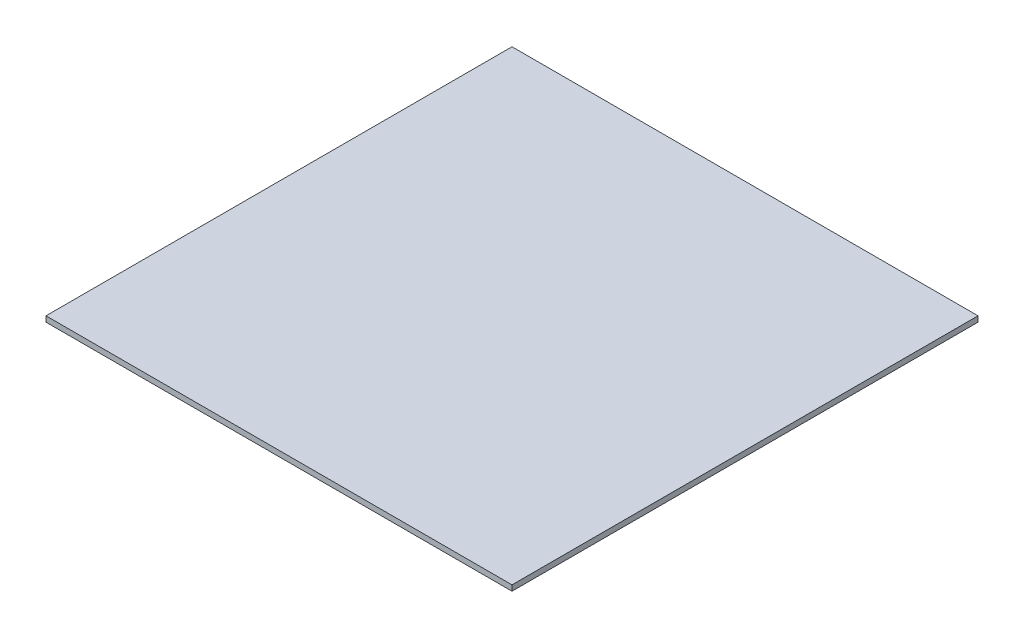
SolidWorks part; units mm, degrees
ref_plane "Front Plane" through (0, 0, 0) normal (0, 0, 1) x (1, 0, 0)
ref_plane "Top Plane" through (0, 0, 0) normal (0, 1, 0) x (1, 0, 0)
ref_plane "Right Plane" through (0, 0, 0) normal (1, 0, 0) x (0, 0, -1)
sketch "Sketch1" plane through (0, 0, 0) normal (0, 1, 0) x (1, 0, 0)
  line L1 (0, 0) -> (133.35, 0)
  line L2 (0, 0) -> (0, 133.35)
  line L3 (0, 133.35) -> (133.35, 133.35)
  line L4 (133.35, 0) -> (133.35, 133.35)
  dimension "D1" = 133.35
  dimension "D2" = 133.35
extrude "Boss-Extrude1" add sketch "Sketch1" along normal blind 1.5875
